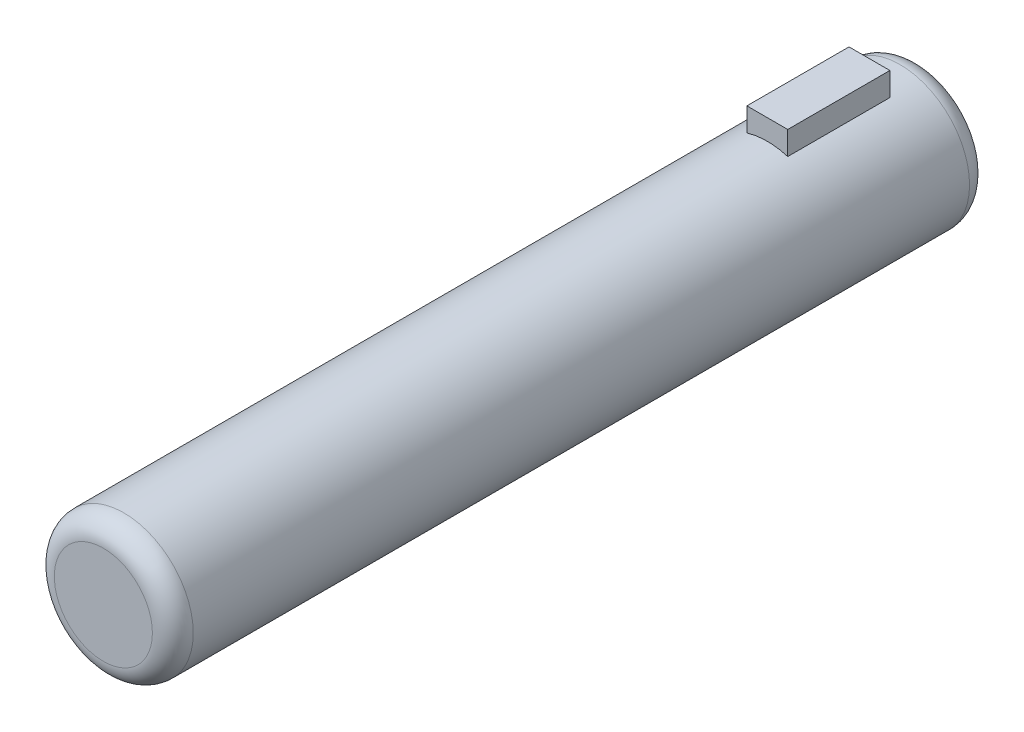
SolidWorks part; units mm, degrees
ref_plane "Front Plane" through (0, 0, 0) normal (0, 0, 1) x (1, 0, 0)
ref_plane "Top Plane" through (0, 0, 0) normal (0, 1, 0) x (1, 0, 0)
ref_plane "Right Plane" through (0, 0, 0) normal (1, 0, 0) x (0, 0, -1)
sketch "Sketch1" plane through (0, 0, 0) normal (0, 0, 1) x (1, 0, 0)
  circle A0 centre (0, 0) radius 3.4
  dimension "D1" = 6.8
extrude "Boss-Extrude1" add sketch "Sketch1" along normal blind 40
fillet "Fillet2" radius 1 2 edges at (3.4, 0, 0) (3.4, 0, 40)
ref_plane "Plane1" through (0, 0, 2.5) normal (0, 0, 1) x (1, 0, 0)
sketch "Sketch2" plane through (0, 0, 2.5) normal (0, 0, 1) x (1, 0, 0)
  line L2 (1, 3.2496) -> (1, 4.3996)
  line L3 (1, 4.3996) -> (-1, 4.3996)
  line L4 (-1, 3.2496) -> (-1, 4.3996)
  circle A1 centre (0, 0) radius 3.4 construction
  arc A2 (1, 3.2496) -> (-1, 3.2496) centre (0, 0) ccw
  point P0 (0, 0)
  point P2 (0, 4.3996)
  dimension "D1" = 2
  dimension "D2" = 1.15
extrude "Boss-Extrude2" add sketch "Sketch2" along normal blind 5
